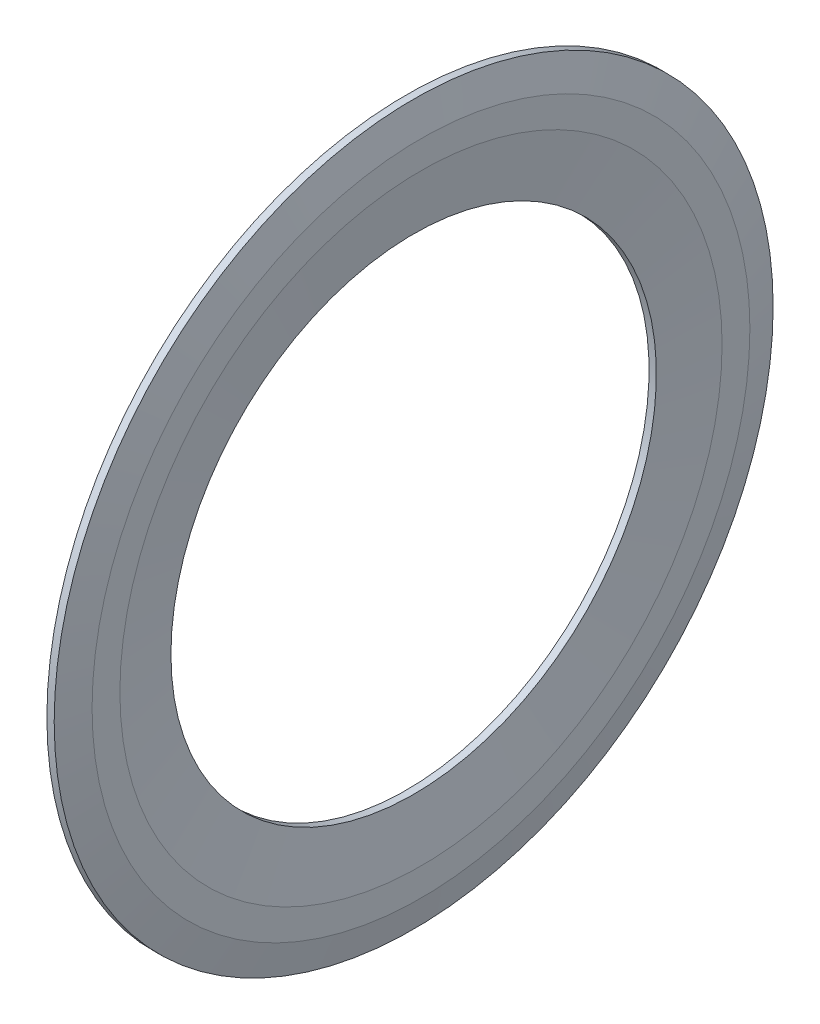
SolidWorks part; units mm, degrees
ref_plane "Front Plane" through (0, 0, 0) normal (0, 0, 1) x (1, 0, 0)
ref_plane "Top Plane" through (0, 0, 0) normal (0, 1, 0) x (1, 0, 0)
ref_plane "Right Plane" through (0, 0, 0) normal (1, 0, 0) x (0, 0, -1)
ref_plane "Plane1" through (0, 0, 0) normal (0, 0, 1) x (1, 0, 0)
sketch "Sketch1" plane through (0, 0, 0) normal (0, 0, 1) x (1, 0, 0)
  line L0 (0.3575, 5.85) -> (0.417, 5.375)
  line L1 (0.417, 5.375) -> (0.3575, 4.9)
  line L2 (0.3575, 4.9) -> (0.3575, 3.95)
  line L3 (0.3575, 3.95) -> (0.4766, 3.95)
  line L4 (0.4766, 3.95) -> (0.5958, 4.9)
  line L5 (0.5958, 4.9) -> (0.5958, 5.3526)
  line L6 (0.5958, 5.3526) -> (0.4766, 5.85)
  line L7 (0.4766, 5.85) -> (0.3575, 5.85)
  line L8 (0.4766, 0) -> (0.3575, 0) construction
revolve "Revolve1" add sketch "Sketch1" angle 360 about L8
